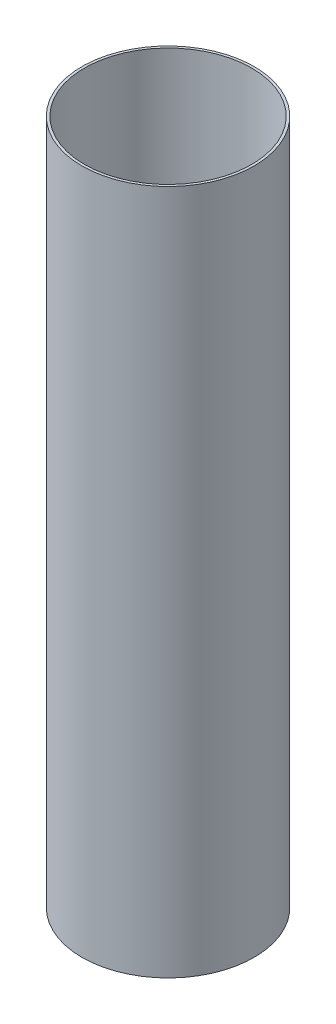
SolidWorks part; units mm, degrees
ref_plane "Front Plane" through (0, 0, 0) normal (0, 0, 1) x (1, 0, 0)
ref_plane "Top Plane" through (0, 0, 0) normal (0, 1, 0) x (1, 0, 0)
ref_plane "Right Plane" through (0, 0, 0) normal (1, 0, 0) x (0, 0, -1)
sketch "Sketch1" plane through (0, 0, 0) normal (0, 1, 0) x (1, 0, 0)
  circle A0 centre (0, 0) radius 63.5
  circle A1 centre (0, 0) radius 65.405
  dimension "D1" = 130.81
  dimension "D2" = 127
extrude "Boss-Extrude1" add sketch "Sketch1" along normal mid plane 520.7
equation "\"iDiameter\"= 5in"
equation "\"oDiameter\"= 5.15in"
equation "\"length\"= 20.5in"
